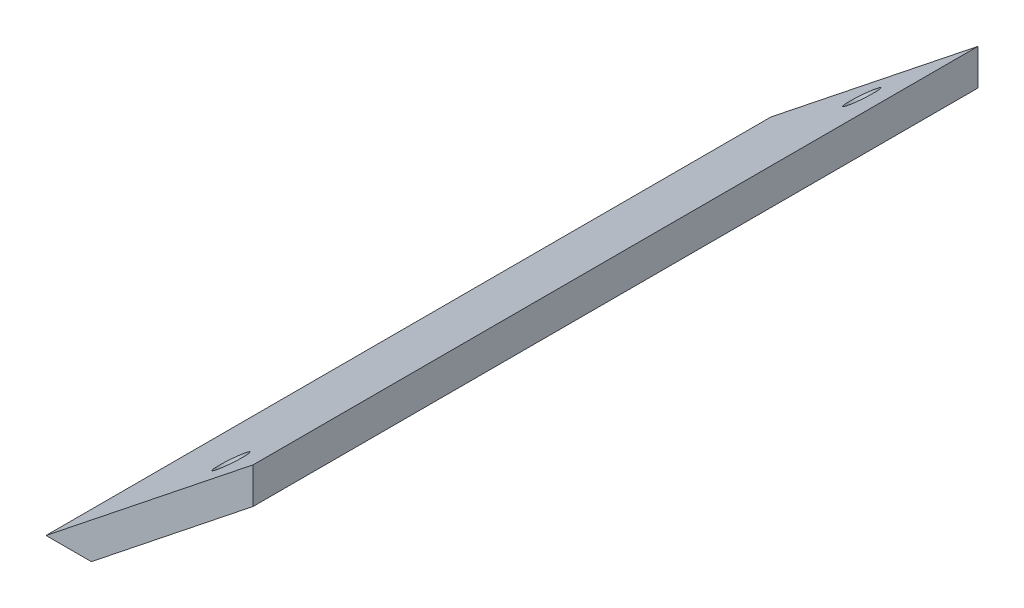
SolidWorks part; units mm, degrees
ref_plane "Alzado" through (0, 0, 0) normal (0, 0, 1) x (1, 0, 0)
ref_plane "Planta" through (0, 0, 0) normal (0, 1, 0) x (1, 0, 0)
ref_plane "Vista lateral" through (0, 0, 0) normal (1, 0, 0) x (0, 0, -1)
sketch "Croquis1" plane through (0, 0, 0) normal (0, 0, 1) x (1, 0, 0)
  line L0 (-22, 0) -> (-17.1809, 0)
  line L1 (-17.1809, 0) -> (0, 13.6666)
  line L2 (0, 13.6666) -> (0, 17.5)
  line L3 (0, 17.5) -> (-22, 0)
  dimension "D1" = 3
  dimension "D2" = 17.5
  dimension "D3" = 22
extrude "Saliente-Extruir1" add sketch "Croquis1" along normal blind 77
sketch "Croquis2" plane through (-8.5258, 10.7181, 0) normal (-0.6225, 0.7826, 0) x (0.7826, 0.6225, 0)
  line L0 (1.5078, 0) -> (1.5078, -77) construction
  line L1 (10.8942, 0) -> (-17.2172, 0) construction
  line L2 (10.8942, -77) -> (-17.2172, -77) construction
  line L3 (8.5078, -77) -> (8.5078, 0) construction
  line L4 (8.5078, -77) -> (8.5078, 0) construction
  circle A0 centre (1.5078, -5) radius 1.6
  circle A1 centre (1.5078, -72) radius 1.6
  dimension "D1" = 3.2
  dimension "D2" = 5
  dimension "D3" = 5
  dimension "D4" = 7
extrude "Cortar-Extruir1" cut sketch "Croquis2" against normal up to next
